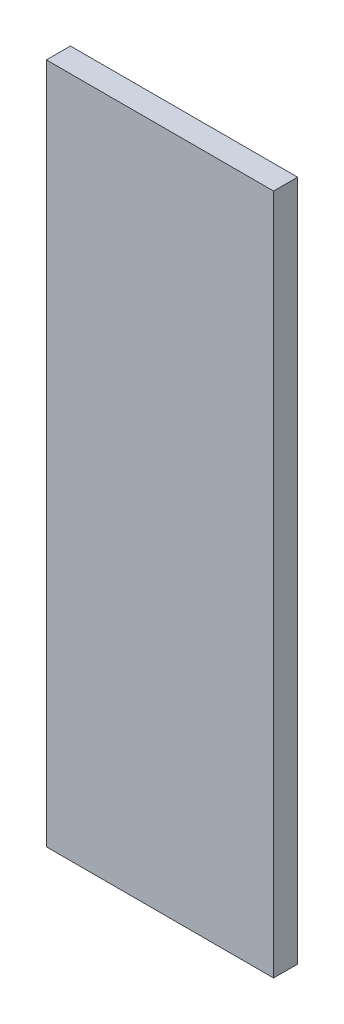
SolidWorks part; units mm, degrees
ref_plane "Front Plane" through (0, 0, 0) normal (0, 0, 1) x (1, 0, 0)
ref_plane "Top Plane" through (0, 0, 0) normal (0, 1, 0) x (1, 0, 0)
ref_plane "Right Plane" through (0, 0, 0) normal (1, 0, 0) x (0, 0, -1)
sketch "Sketch1" plane through (0, 0, 0) normal (0, 0, 1) x (1, 0, 0)
  line L1 (15, -45) -> (-15, -45)
  line L2 (15, -45) -> (15, 45)
  line L3 (15, 45) -> (-15, 45)
  line L4 (-15, -45) -> (-15, 45)
  line L5 (15, -45) -> (-15, 45) construction
  line L6 (15, 45) -> (-15, -45) construction
  point P0 (0, 0)
  dimension "D1" = 30
  dimension "D2" = 90
extrude "Boss-Extrude1" add sketch "Sketch1" along normal blind 3.175
